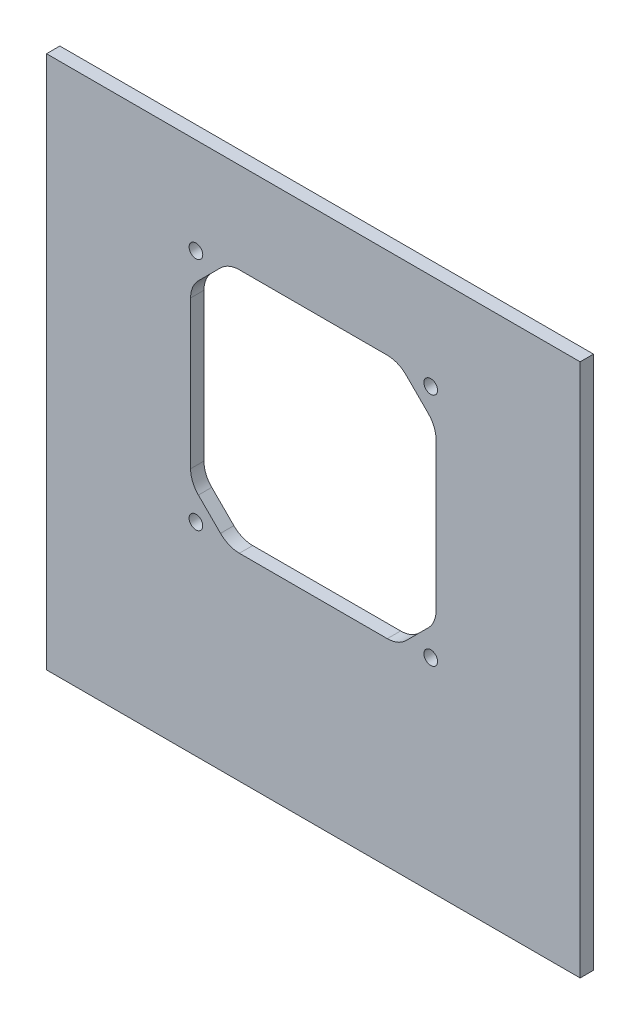
SolidWorks part; units mm, degrees
ref_plane "Front Plane" through (0, 0, 0) normal (0, 0, 1) x (1, 0, 0)
ref_plane "Top Plane" through (0, 0, 0) normal (0, 1, 0) x (1, 0, 0)
ref_plane "Right Plane" through (0, 0, 0) normal (1, 0, 0) x (0, 0, -1)
sketch "Sketch2" plane through (0, 0, 0) normal (0, 0, 1) x (1, 0, 0)
  line L1 (0, 0) -> (254, 0)
  line L2 (0, 0) -> (0, 254)
  line L3 (0, 254) -> (254, 254)
  line L4 (254, 0) -> (254, 254)
  dimension "D1" = 254
  dimension "D2" = 254
extrude "Boss-Extrude1" add sketch "Sketch2" along normal blind 6.35
sketch "Sketch3" plane through (0, 0, 6.35) normal (0, 0, 1) x (1, 0, 0)
  line L0 (254, 254) -> (0, 254) construction
  line L1 (0, 254) -> (0, 0) construction
  line L2 (72.2997, 196.5792) -> (82.8208, 207.1003)
  line L3 (91.801, 210.82) -> (162.199, 210.82)
  line L4 (68.58, 187.599) -> (68.58, 117.201)
  line L5 (91.801, 93.98) -> (162.199, 93.98)
  line L6 (185.42, 187.599) -> (185.42, 117.201)
  line L7 (171.1792, 207.1003) -> (181.7003, 196.5792)
  line L8 (181.7003, 108.2208) -> (171.1792, 97.6997)
  line L9 (72.2997, 108.2208) -> (82.8208, 97.6997)
  circle A0 centre (127, 152.4) radius 44.45 construction
  arc A1 (171.1792, 207.1003) -> (162.199, 210.82) centre (162.199, 198.12) ccw
  arc A2 (181.7003, 196.5792) -> (185.42, 187.599) centre (172.72, 187.599) cw
  arc A3 (181.7003, 108.2208) -> (185.42, 117.201) centre (172.72, 117.201) ccw
  arc A4 (171.1792, 97.6997) -> (162.199, 93.98) centre (162.199, 106.68) cw
  arc A5 (82.8208, 97.6997) -> (91.801, 93.98) centre (91.801, 106.68) ccw
  arc A6 (72.2997, 108.2208) -> (68.58, 117.201) centre (81.28, 117.201) cw
  arc A7 (72.2997, 196.5792) -> (68.58, 187.599) centre (81.28, 187.599) ccw
  arc A8 (82.8208, 207.1003) -> (91.801, 210.82) centre (91.801, 198.12) cw
  circle A9 centre (71.12, 208.28) radius 3.25
  circle A10 centre (182.88, 208.28) radius 3.25
  circle A11 centre (182.88, 96.52) radius 3.25
  circle A12 centre (71.12, 96.52) radius 3.25
  point P8 (167.4595, 210.82)
  point P19 (185.42, 192.8595)
  point P22 (185.42, 111.9405)
  point P25 (167.4595, 93.98)
  point P28 (86.5405, 93.98)
  point P31 (68.58, 111.9405)
  point P34 (68.58, 192.8595)
  point P37 (86.5405, 210.82)
  point P46 (72.2997, 207.1003)
  point P47 (181.7003, 207.1003)
  point P48 (0, 0)
  point P49 (72.2997, 97.6997)
  point P50 (0, 0)
  point P51 (0, 0)
  point P52 (111.0276, 93.98)
  dimension "D1" = 88.9
  dimension "D4" = 12.7
  dimension "D5" = 6.5
  dimension "D16" = 6.5
  dimension "D17" = 6.5
  dimension "D18" = 6.5
  dimension "D2" = 101.6
  dimension "D3" = 127
  dimension "D6" = 58.42
  dimension "D7" = 58.42
  dimension "D8" = 25.4
  dimension "D9" = 25.4
  dimension "D10" = 25.4
  dimension "D11" = 25.4
  dimension "D12" = 45
  dimension "D13" = 135
  dimension "D14" = 45
  dimension "D15" = 135
  dimension "D19" = 2.54
  dimension "D20" = 2.54
  dimension "D21" = 2.54
  dimension "D22" = 2.54
  dimension "D23" = 2.54
  dimension "D24" = 2.54
  dimension "D25" = 2.54
  dimension "D26" = 2.54
extrude "Cut-Extrude1" cut sketch "Sketch3" against normal blind 6.35
equation "\"D16@Sketch3\"=\"D5@Sketch3\""
equation "\"D17@Sketch3\"=\"D5@Sketch3\""
equation "\"D18@Sketch3\"=\"D5@Sketch3\""
